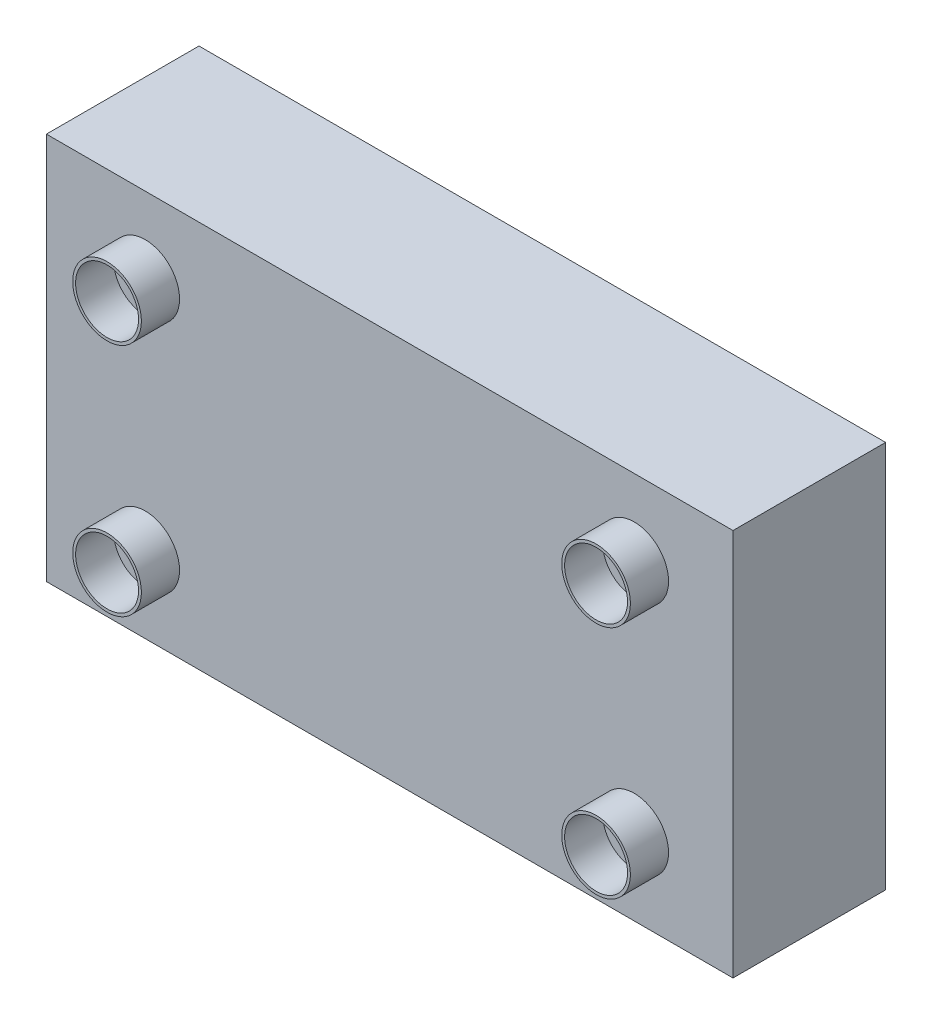
SolidWorks part; units mm, degrees
ref_plane "Front Plane" through (0, 0, 0) normal (0, 0, 1) x (1, 0, 0)
ref_plane "Top Plane" through (0, 0, 0) normal (0, 1, 0) x (1, 0, 0)
ref_plane "Right Plane" through (0, 0, 0) normal (1, 0, 0) x (0, 0, -1)
sketch "Sketch1" plane through (0, 0, 0) normal (0, 0, 1) x (1, 0, 0)
  line L1 (90, -50.8) -> (-90, -50.8)
  line L2 (90, -50.8) -> (90, 50.8)
  line L3 (90, 50.8) -> (-90, 50.8)
  line L4 (-90, -50.8) -> (-90, 50.8)
  line L5 (90, -50.8) -> (-90, 50.8) construction
  line L6 (90, 50.8) -> (-90, -50.8) construction
  point P0 (0, 0)
  dimension "D1" = 180
  dimension "D2" = 101.6
extrude "Boss-Extrude1" add sketch "Sketch1" along normal blind 40
sketch "Sketch3" plane through (0, 0, 0) normal (0, 0, -1) x (-1, 0, 0)
  line L1 (80, -40.8) -> (-80, -40.8)
  line L2 (80, -40.8) -> (80, 40.8)
  line L3 (80, 40.8) -> (-80, 40.8)
  line L4 (-80, -40.8) -> (-80, 40.8)
  line L5 (80, -40.8) -> (-80, 40.8) construction
  line L6 (80, 40.8) -> (-80, -40.8) construction
  line L7 (-90, -50.8) -> (-90, 50.8) construction
  line L8 (-90, 50.8) -> (90, 50.8) construction
  point P0 (0, 0)
  dimension "D1" = 10
  dimension "D2" = 10
extrude "Cut-Extrude3" cut sketch "Sketch3" against normal blind 5
sketch "Sketch4" plane through (0, 0, 40) normal (0, 0, 1) x (1, 0, 0)
  line L0 (90, 50.8) -> (-90, 50.8) construction
  line L1 (-90, 50.8) -> (-90, -50.8) construction
  line L2 (-90, -50.8) -> (90, -50.8) construction
  line L3 (90, -50.8) -> (90, 50.8) construction
  circle A0 centre (-64.1, 30.8) radius 9
  circle A1 centre (-64.1, -30.8) radius 9
  circle A2 centre (64.1, 30.8) radius 9
  circle A3 centre (64.1, -30.8) radius 9
  dimension "D1" = 18
  dimension "D2" = 20
  dimension "D3" = 25.9
  dimension "D4" = 18
  dimension "D5" = 25.9
  dimension "D6" = 20
  dimension "D7" = 18
  dimension "D8" = 20
  dimension "D9" = 25.9
  dimension "D10" = 18
  dimension "D11" = 25.9
  dimension "D12" = 20
extrude "Boss-Extrude2" add sketch "Sketch4" along normal blind 10
sketch "Sketch5" plane through (0, 0, 50) normal (0, 0, 1) x (1, 0, 0)
  circle A0 centre (-64.1, 30.8) radius 8.25
  circle A1 centre (64.1, 30.8) radius 8.25
  circle A2 centre (64.1, -30.8) radius 8.25
  circle A3 centre (-64.1, -30.8) radius 8.25
  dimension "D1" = 16.5
  dimension "D2" = 16.5
  dimension "D3" = 16.5
  dimension "D4" = 16.5
extrude "Cut-Extrude4" cut sketch "Sketch5" against normal blind 10
